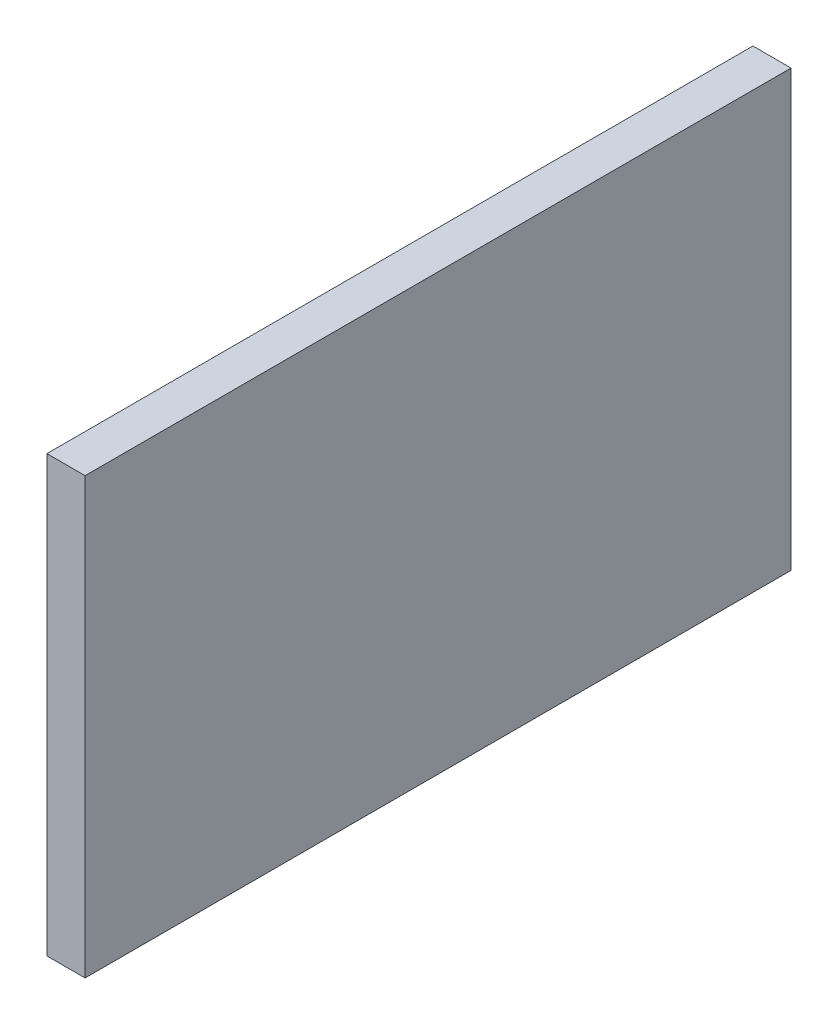
SolidWorks part; units mm, degrees
ref_plane "前视基准面" through (0, 0, 0) normal (0, 0, 1) x (1, 0, 0)
ref_plane "上视基准面" through (0, 0, 0) normal (0, 1, 0) x (1, 0, 0)
ref_plane "右视基准面" through (0, 0, 0) normal (1, 0, 0) x (0, 0, -1)
sketch "草图1" plane through (0, 0, 0) normal (1, 0, 0) x (0, 0, -1)
  line L1 (-92.5, 57) -> (92.5, 57)
  line L2 (-92.5, 57) -> (-92.5, -57)
  line L3 (-92.5, -57) -> (92.5, -57)
  line L4 (92.5, 57) -> (92.5, -57)
  line L5 (-92.5, 57) -> (92.5, -57) construction
  line L6 (-92.5, -57) -> (92.5, 57) construction
  point P0 (0, 0)
  dimension "D1" = 185
  dimension "D2" = 114
extrude "凸台-拉伸1" add sketch "草图1" along normal blind 10
